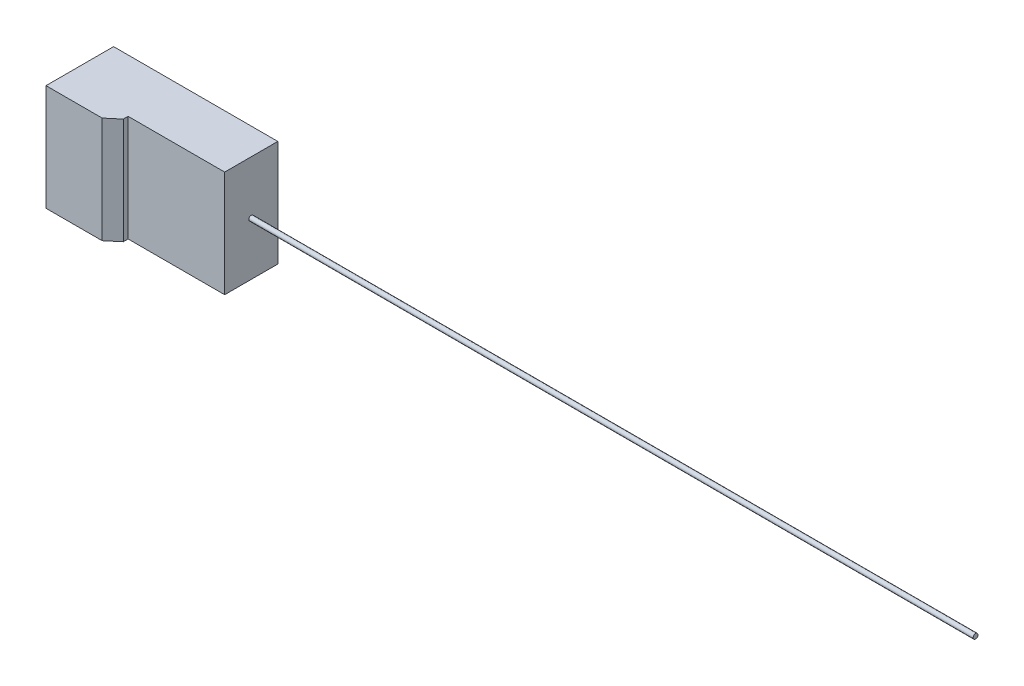
SolidWorks part; units mm, degrees
ref_plane "Alzado" through (0, 0, 0) normal (0, 0, 1) x (1, 0, 0)
ref_plane "Planta" through (0, 0, 0) normal (0, 1, 0) x (1, 0, 0)
ref_plane "Vista lateral" through (0, 0, 0) normal (1, 0, 0) x (0, 0, -1)
sketch "Croquis1" plane through (0, 0, 0) normal (0, 0, 1) x (1, 0, 0)
  line L1 (-17, 11) -> (17, 11)
  line L2 (-17, 11) -> (-17, -11)
  line L3 (-17, -11) -> (17, -11)
  line L4 (17, 11) -> (17, -11)
  line L5 (-17, 11) -> (17, -11) construction
  line L6 (-17, -11) -> (17, 11) construction
  point P0 (0, 0)
  dimension "D1" = 34
  dimension "D2" = 22
extrude "Saliente-Extruir1" add sketch "Croquis1" along normal blind 11
sketch "Croquis2" plane through (0, 0, 11) normal (0, 0, 1) x (1, 0, 0)
  line L0 (-17, -11) -> (17, -11) construction
  line L1 (-17, 11) -> (-3, 11)
  line L2 (-17, 11) -> (-17, -11)
  line L3 (-17, -11) -> (-3, -11)
  line L4 (-3, 11) -> (-3, -11)
  dimension "D1" = 14
extrude "Saliente-Extruir2" add sketch "Croquis2" along normal blind 3
chamfer "Chaflán1" distance 2 angle 50 1 edges at (-3, 0, 14)
sketch "Croquis3" plane through (17, 0, 0) normal (1, 0, 0) x (0, 0, -1)
  line L0 (-5.5, -11) -> (-5.5, 11) construction
  line L1 (-11, -11) -> (0, -11) construction
  line L2 (0, 0) -> (-11, 0) construction
  line L3 (-11, -11) -> (-11, 11) construction
  line L4 (-11, 11) -> (0, 11) construction
  circle A0 centre (-5.5, 0) radius 0.5
  dimension "D1" = 1
extrude "Saliente-Extruir3" add sketch "Croquis3" along normal blind 150
